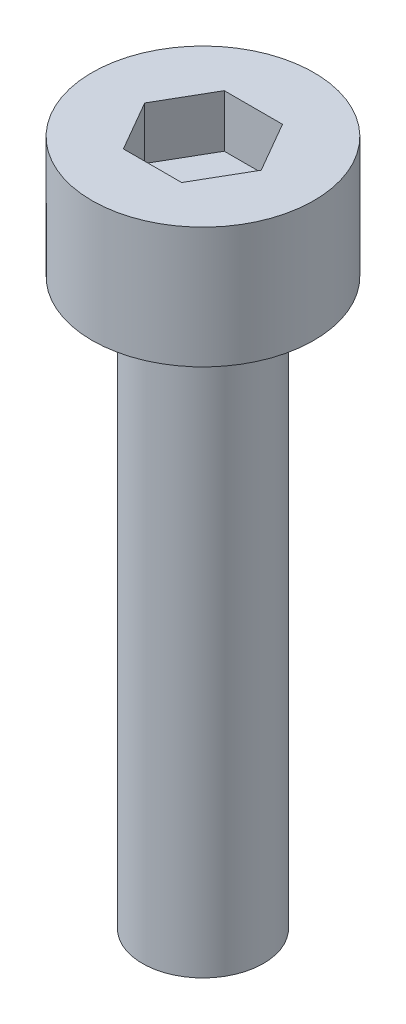
SolidWorks part; units mm, degrees
material "AISI 304"
ref_plane "前视基准面" through (0, 0, 0) normal (0, 0, 1) x (1, 0, 0)
ref_plane "上视基准面" through (0, 0, 0) normal (0, 1, 0) x (1, 0, 0)
ref_plane "右视基准面" through (0, 0, 0) normal (1, 0, 0) x (0, 0, -1)
sketch "草图1" plane through (0, 0, 0) normal (0, 1, 0) x (1, 0, 0)
  circle A0 centre (0, 0) radius 2.75
  dimension "D1" = 5.5
extrude "杯头" add sketch "草图1" along normal blind 3
sketch "草图2" plane through (0, 3, 0) normal (0, 1, 0) x (1, 0, 0)
  line L1 (1.4434, 0) -> (0.7217, 1.25)
  line L2 (0.7217, 1.25) -> (-0.7217, 1.25)
  line L3 (-0.7217, 1.25) -> (-1.4434, 0)
  line L4 (-1.4434, 0) -> (-0.7217, -1.25)
  line L5 (-0.7217, -1.25) -> (0.7217, -1.25)
  line L6 (0.7217, -1.25) -> (1.4434, 0)
  circle A0 centre (0, 0) radius 1.25 construction
  dimension "D1" = 2.5
extrude "内六角口" cut sketch "草图2" against normal blind 1.3
sketch "草图3" plane through (0, 0, 0) normal (0, -1, 0) x (1, 0, 0)
  circle A0 centre (0, 0) radius 1.5
  dimension "D1" = 3
extrude "螺纹长" add sketch "草图3" along normal blind 14
